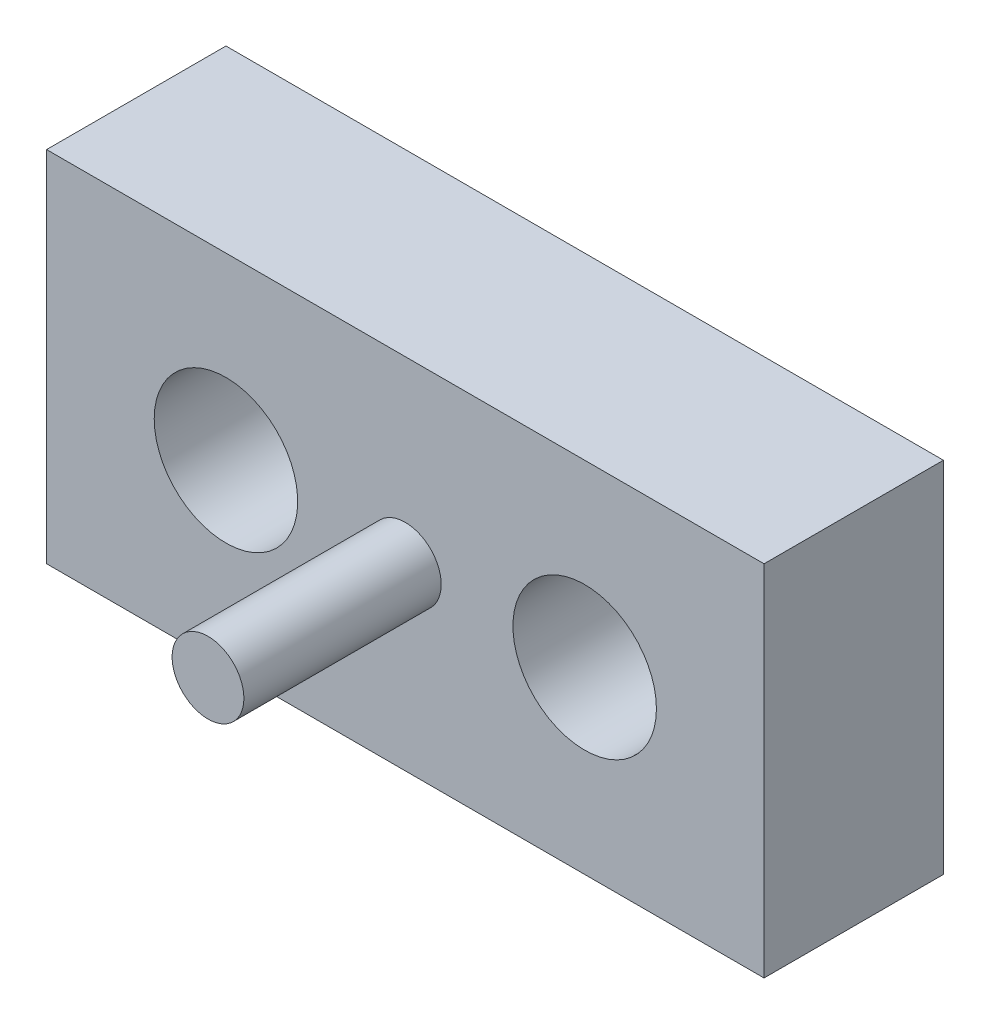
SolidWorks part; units mm, degrees
ref_plane "前视基准面" through (0, 0, 0) normal (0, 0, 1) x (1, 0, 0)
ref_plane "上视基准面" through (0, 0, 0) normal (0, 1, 0) x (1, 0, 0)
ref_plane "右视基准面" through (0, 0, 0) normal (1, 0, 0) x (0, 0, -1)
sketch "草图1" plane through (0, 0, 0) normal (0, 0, 1) x (1, 0, 0)
  line L0 (0, 0) -> (0, -21.9567) construction
  line L1 (-10, 5) -> (10, 5)
  line L2 (-10, 5) -> (-10, -5)
  line L3 (-10, -5) -> (10, -5)
  line L4 (10, 5) -> (10, -5)
  line L5 (-10, 5) -> (10, -5) construction
  line L6 (-10, -5) -> (10, 5) construction
  circle A0 centre (-5, 0) radius 1
  circle A1 centre (5, 0) radius 1
  point P0 (0, 0)
  dimension "D1" = 2
  dimension "D2" = 20
  dimension "D3" = 10
  dimension "D4" = 5
extrude "凸台-拉伸1" add sketch "草图1" along normal blind 5
sketch "草图2" plane through (0, 0, 5) normal (0, 0, 1) x (1, 0, 0)
  circle A0 centre (0, 0) radius 1
  dimension "D1" = 2
extrude "凸台-拉伸2" add sketch "草图2" along normal blind 5.5
sketch "草图4" plane through (0, 0, 5) normal (0, 0, 1) x (1, 0, 0)
  line L0 (0, 0) -> (0, -7.3571) construction
  circle A0 centre (5, 0) radius 2
  circle A1 centre (-5, 0) radius 2
  dimension "D1" = 4
extrude "切除-拉伸2" cut sketch "草图4" against normal blind 3
